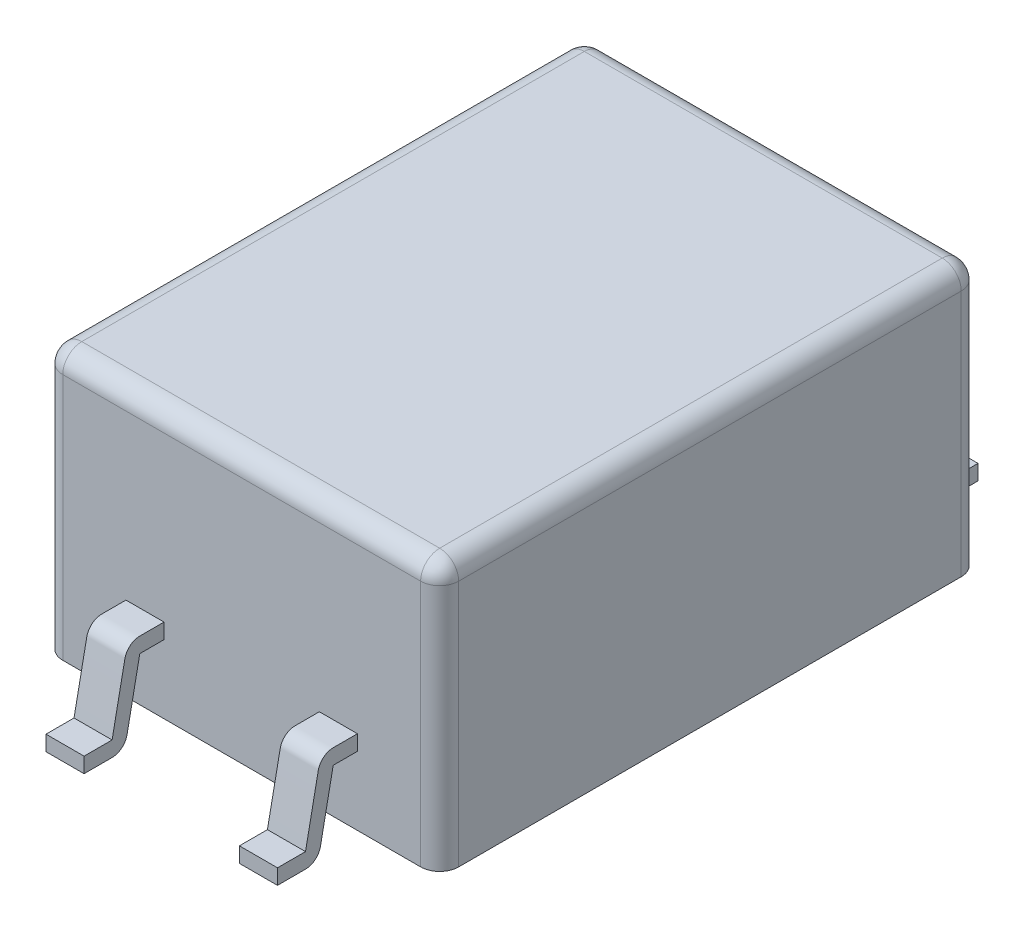
SolidWorks part; units mm, degrees
ref_plane "Спереди" through (0, 0, 0) normal (0, 0, 1) x (1, 0, 0)
ref_plane "Сверху" through (0, 0, 0) normal (0, 1, 0) x (1, 0, 0)
ref_plane "Справа" through (0, 0, 0) normal (1, 0, 0) x (0, 0, -1)
sketch "Эскиз1" plane through (0, 0, 0) normal (0, 1, 0) x (1, 0, 0)
  line L1 (-2.35, -3.55) -> (2.35, -3.55)
  line L2 (-2.6, -3.3) -> (-2.6, 3.3)
  line L3 (-2.35, 3.55) -> (2.35, 3.55)
  line L4 (2.6, -3.3) -> (2.6, 3.3)
  line L5 (-2.6, -3.55) -> (2.6, 3.55) construction
  line L6 (-2.6, 3.55) -> (2.6, -3.55) construction
  arc A0 (-2.35, -3.55) -> (-2.6, -3.3) centre (-2.35, -3.3) cw
  arc A1 (2.35, -3.55) -> (2.6, -3.3) centre (2.35, -3.3) ccw
  arc A2 (2.35, 3.55) -> (2.6, 3.3) centre (2.35, 3.3) cw
  arc A3 (-2.6, 3.3) -> (-2.35, 3.55) centre (-2.35, 3.3) cw
  point P0 (0, 0)
  dimension "D1" = 0.25
  dimension "D2" = 7.1
  dimension "D3" = 5.2
extrude "Бобышка-Вытянуть1" add sketch "Эскиз1" along normal blind 3.5
fillet "Скругление1" radius 0.25 8 edges at (-2.5268, 3.5, 3.4768) (-2.6, 3.5, 0) (-2.5268, 3.5, -3.4768) (0, 3.5, -3.55) (2.5268, 3.5, -3.4768) (2.6, 3.5, 0) (2.5268, 3.5, 3.4768) (0, 3.5, 3.55)
ref_plane "Плоскость1" through (1.27, 0, 0) normal (1, 0, 0) x (0, 0, -1)
sketch "Эскиз3" plane through (1.27, 0, 0) normal (1, 0, 0) x (0, 0, -1)
  line L0 (-3.55, 1) -> (-3.868, 1)
  line L1 (-3.55, 3.25) -> (-3.55, 0) construction
  line L2 (-3.9661, 0.9196) -> (-4.1339, 0.0804)
  line L3 (-4.232, 0) -> (-4.6, 0)
  arc A0 (-4.1339, 0.0804) -> (-4.232, 0) centre (-4.232, 0.1) cw
  arc A1 (-3.868, 1) -> (-3.9661, 0.9196) centre (-3.868, 0.9) ccw
  point P1 (0, 0)
  dimension "D1" = 0.1
  dimension "D2" = 0.1
sketch "Эскиз4" plane through (0, 0, 3.55) normal (0, 0, 1) x (1, 0, 0)
  line L1 (1.02, 1.1) -> (1.52, 1.1)
  line L2 (1.02, 1.1) -> (1.02, 0.9)
  line L3 (1.02, 0.9) -> (1.52, 0.9)
  line L4 (1.52, 1.1) -> (1.52, 0.9)
  line L5 (1.02, 1.1) -> (1.52, 0.9) construction
  line L6 (1.02, 0.9) -> (1.52, 1.1) construction
  point P0 (1.27, 1)
sweep "По траектории3" add profiles "Эскиз4" path "Эскиз3"
mirror "Зеркальное отражение1" about plane through (0, 0, 0) normal (0, 0, 1) of "По траектории3"
mirror "Зеркальное отражение2" about plane through (0, 0, 0) normal (1, 0, 0) of "Зеркальное отражение1", "По траектории3"
